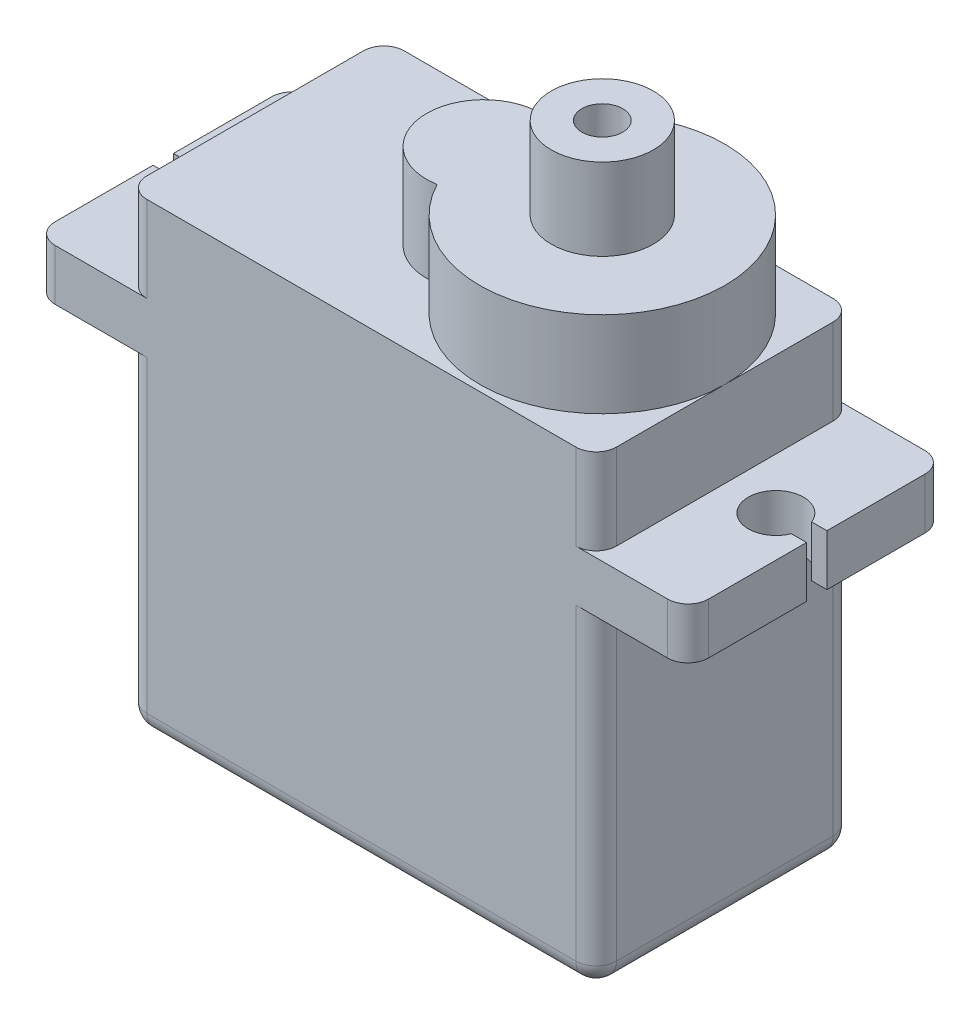
SolidWorks part; units mm, degrees
ref_plane "Front Plane" through (0, 0, 0) normal (0, 0, 1) x (1, 0, 0)
ref_plane "Top Plane" through (0, 0, 0) normal (0, 1, 0) x (1, 0, 0)
ref_plane "Right Plane" through (0, 0, 0) normal (1, 0, 0) x (0, 0, -1)
sketch "Sketch1" plane through (0, 0, 0) normal (0, 1, 0) x (1, 0, 0)
  line L1 (-11.5, 6.3) -> (11.5, 6.3)
  line L2 (-11.5, 6.3) -> (-11.5, -6.3)
  line L3 (-11.5, -6.3) -> (11.5, -6.3)
  line L4 (11.5, 6.3) -> (11.5, -6.3)
  line L5 (-11.5, 6.3) -> (11.5, -6.3) construction
  line L6 (-11.5, -6.3) -> (11.5, 6.3) construction
  point P0 (0, 0)
  dimension "D1" = 12.6
  dimension "D2" = 23
extrude "Boss-Extrude1" add sketch "Sketch1" along normal blind 22.8
sketch "Sketch2" plane through (0, 22.8, 0) normal (0, 1, 0) x (1, 0, 0)
  line L0 (11.5, -6.3) -> (11.5, 6.3) construction
  line L1 (11.5, -6.3) -> (11.5, 6.3) construction
  arc A0 (0.1724, -2.7599) -> (0.1724, 2.7599) centre (5.5, 0) ccw
  arc A1 (0.1724, 2.7599) -> (0.1724, -2.7599) centre (-0.3, 0) ccw
  dimension "D1" = 12
  dimension "D2" = 5.6
  dimension "D3" = 11.8
extrude "Boss-Extrude2" add sketch "Sketch2" along normal blind 4.2
sketch "Sketch3" plane through (0, 27, 0) normal (0, 1, 0) x (1, 0, 0)
  circle A0 centre (5.5, 0) radius 2.5
  dimension "D1" = 5
extrude "Extrude-Thin1" add sketch "Sketch3" along normal blind 4 thin thin type one direction reverse wall 1.5
fillet "Fillet1" radius 1 8 edges at (0, 0, -6.3) (11.5, 0, 0) (0, 0, 6.3) (-11.5, 0, 0) (-11.5, 11.4, -6.3) (11.5, 11.4, -6.3) (11.5, 11.4, 6.3) (-11.5, 11.4, 6.3)
sketch "Sketch4" plane through (0, 22.8, 0) normal (0, 1, 0) x (1, 0, 0)
  line L0 (-9.1077, 6.3) -> (-16, 6.3)
  line L1 (10.5, 6.3) -> (-10.5, 6.3) construction
  line L2 (-16, 6.3) -> (-16, 0.5)
  line L3 (-16, -6.3) -> (-9.1077, -6.3)
  line L4 (-10.5, -6.3) -> (10.5, -6.3) construction
  line L5 (-9.1077, -6.3) -> (-9.1077, 6.3)
  line L6 (-16, 0.5) -> (-15.254, 0.5)
  line L7 (-16, -0.5) -> (-15.254, -0.5)
  line L8 (-16, -0.5) -> (-16, -6.3)
  arc A0 (-15.254, -0.5) -> (-15.254, 0.5) centre (-14, 0) ccw
  dimension "D2" = 2.7
  dimension "D1" = 16
  dimension "D3" = 14
  dimension "D4" = 1
extrude "Boss-Extrude4" add sketch "Sketch4" against normal blind 2.5 from offset 4.2 offset against normal yes
fillet "Fillet2" radius 1 2 edges at (-16, 17.35, -6.3) (-16, 17.35, 6.3)
mirror "Mirror1" about plane through (0, 0, 0) normal (1, 0, 0) of "Boss-Extrude4", "Fillet2"
